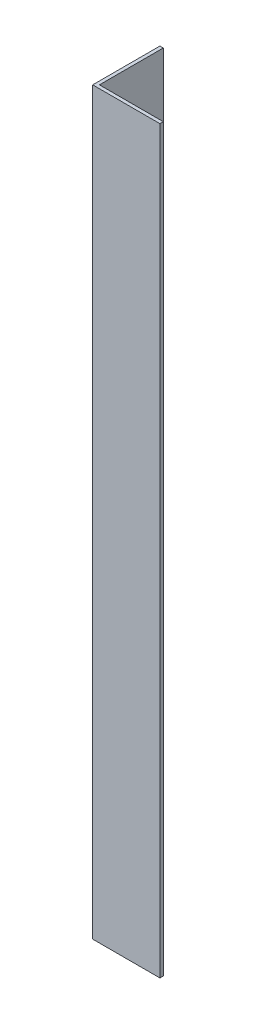
SolidWorks part; units mm, degrees
material "1060 Сплав"
ref_plane "Спереди" through (0, 0, 0) normal (0, 0, 1) x (1, 0, 0)
ref_plane "Сверху" through (0, 0, 0) normal (0, 1, 0) x (1, 0, 0)
ref_plane "Справа" through (0, 0, 0) normal (1, 0, 0) x (0, 0, -1)
sketch "Эскиз1" plane through (0, 0, 0) normal (0, 1, 0) x (1, 0, 0)
  line L0 (0, 0) -> (0, 20)
  line L1 (0, 20) -> (1, 20)
  line L2 (1, 20) -> (1, 1)
  line L3 (1, 1) -> (20, 1)
  line L4 (20, 1) -> (20, 0)
  line L5 (20, 0) -> (0, 0)
  dimension "D1" = 1
  dimension "D2" = 20
extrude "Бобышка-Вытянуть1" add sketch "Эскиз1" along normal blind 220
sketch "Эскиз2" plane through (1, 0, 0) normal (1, 0, 0) x (0, 0, -1)
  line L0 (10.5, 220) -> (10.5, 0) construction
  line L1 (1, 220) -> (20, 220) construction
  line L2 (1, 0) -> (20, 0) construction
  circle A0 centre (10.5, 180) radius 4.25
  circle A1 centre (10.5, 110) radius 4.25
  circle A2 centre (10.5, 40) radius 4.25
  dimension "D1" = 40
  dimension "D2" = 8.5
  dimension "D4" = 70
  dimension "D5" = 40
  dimension "D3" = 3
extrude "Вырез-Вытянуть1" cut sketch "Эскиз2" against normal through all
